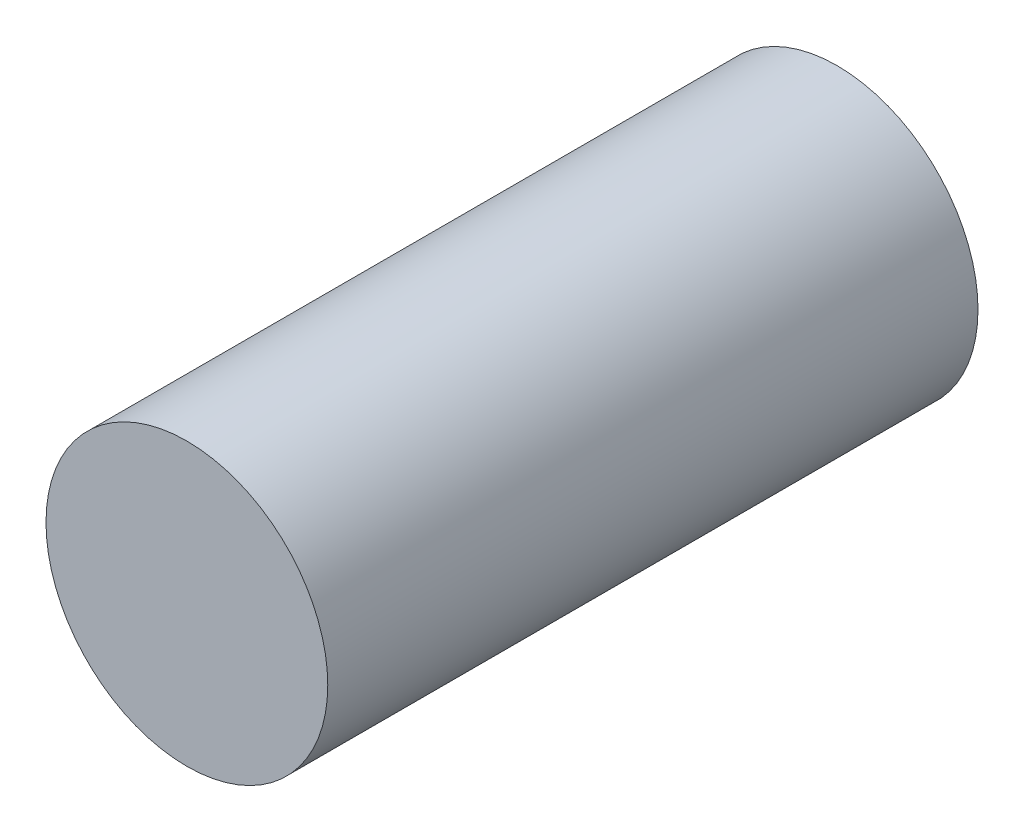
SolidWorks part; units mm, degrees
material "BUTYL"
ref_plane "Front" through (0, 0, 0) normal (0, 0, 1) x (1, 0, 0)
ref_plane "Top" through (0, 0, 0) normal (0, 1, 0) x (1, 0, 0)
ref_plane "Right" through (0, 0, 0) normal (1, 0, 0) x (0, 0, -1)
sketch "Sketch1" plane through (0, 0, 0) normal (0, 0, 1) x (1, 0, 0)
  circle A0 centre (0, 0) radius 6.5
  dimension "D1" = 13
extrude "Boss-Extrude1" add sketch "Sketch1" along normal blind 30
